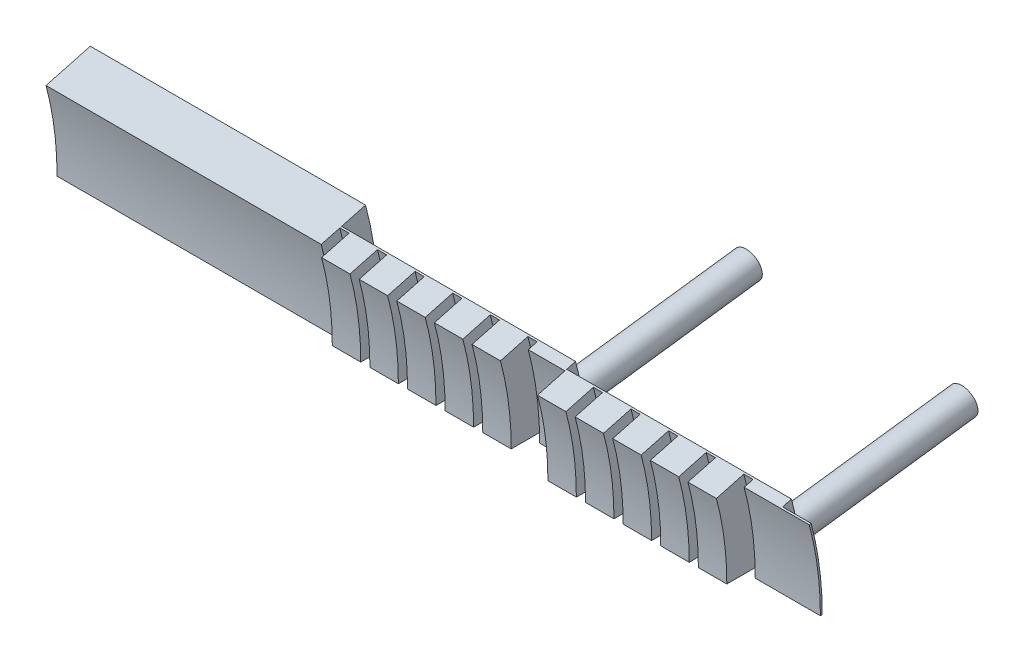
SolidWorks part; units mm, degrees
ref_plane "Front Plane" through (0, 0, 0) normal (0, 0, 1) x (1, 0, 0)
ref_plane "Top Plane" through (0, 0, 0) normal (0, 1, 0) x (1, 0, 0)
ref_plane "Right Plane" through (0, 0, 0) normal (1, 0, 0) x (0, 0, -1)
sketch "Sketch1" plane through (0, 0, 0) normal (0, 1, 0) x (1, 0, 0)
  line L0 (0, 0) -> (6.3693, 0) construction
  line L1 (0.254, 9.525) -> (0.254, 8.7376)
  line L2 (0.254, 8.7376) -> (1.0414, 8.7376)
  line L3 (1.0414, 8.7376) -> (1.0414, 9.525)
  line L4 (1.0414, 9.525) -> (1.2954, 9.525)
  line L5 (1.2954, 9.525) -> (1.2954, 8.7376)
  line L6 (1.2954, 8.7376) -> (2.0828, 8.7376)
  line L7 (2.0828, 8.7376) -> (2.0828, 9.525)
  line L8 (2.0828, 9.525) -> (2.3368, 9.525)
  line L9 (2.3368, 9.525) -> (2.3368, 8.7376)
  line L10 (2.3368, 8.7376) -> (3.1242, 8.7376)
  line L11 (3.1242, 8.7376) -> (3.1242, 9.525)
  line L12 (3.1242, 9.525) -> (3.3782, 9.525)
  line L13 (3.3782, 9.525) -> (3.3782, 8.7376)
  line L14 (3.3782, 8.7376) -> (4.1656, 8.7376)
  line L15 (4.1656, 8.7376) -> (4.1656, 9.525)
  line L16 (4.1656, 9.525) -> (4.4196, 9.525)
  line L17 (4.4196, 9.525) -> (4.4196, 8.7376)
  line L18 (4.4196, 8.7376) -> (5.207, 8.7376)
  line L19 (5.207, 8.7376) -> (5.207, 9.525)
  line L20 (5.207, 9.525) -> (5.461, 9.525)
  line L21 (5.461, 9.525) -> (5.461, 9.271)
  line L22 (5.461, 9.271) -> (6.477, 9.271)
  line L23 (6.477, 9.271) -> (6.477, 8.4836)
  line L24 (6.477, 8.4836) -> (7.2644, 8.4836)
  line L25 (7.2644, 8.4836) -> (7.2644, 9.271)
  line L26 (7.2644, 9.271) -> (7.5184, 9.271)
  line L27 (7.5184, 9.271) -> (7.5184, 8.4836)
  line L28 (7.5184, 8.4836) -> (8.3058, 8.4836)
  line L29 (8.3058, 8.4836) -> (8.3058, 9.271)
  line L30 (8.3058, 9.271) -> (8.5598, 9.271)
  line L31 (8.5598, 9.271) -> (8.5598, 8.4836)
  line L32 (8.5598, 8.4836) -> (9.3472, 8.4836)
  line L33 (9.3472, 8.4836) -> (9.3472, 9.271)
  line L34 (9.3472, 9.271) -> (9.6012, 9.271)
  line L35 (9.6012, 9.271) -> (9.6012, 8.4836)
  line L36 (9.6012, 8.4836) -> (10.3886, 8.4836)
  line L37 (10.3886, 8.4836) -> (10.3886, 9.271)
  line L38 (10.3886, 9.271) -> (10.6426, 9.271)
  line L39 (10.6426, 9.271) -> (10.6426, 8.4836)
  line L40 (10.6426, 8.4836) -> (11.43, 8.4836)
  line L41 (11.43, 8.4836) -> (11.43, 9.271)
  line L42 (11.43, 9.271) -> (11.684, 9.271)
  line L43 (11.684, 9.271) -> (11.684, 9.017)
  line L44 (11.684, 9.017) -> (12.7, 9.017)
  line L131 (0.254, 9.525) -> (0, 9.525)
  line L132 (0, 0) -> (0, 9.525) construction
  line L139 (6.477, 9.5758) -> (6.477, 9.3218)
  line L145 (12.7, 9.3218) -> (12.7, 9.0678)
  line L166 (0, 9.525) -> (0, 8.9916)
  line L167 (0, 8.9916) -> (-7.62, 8.9916)
  line L168 (-7.62, 8.9916) -> (-7.62, 10.2616)
  line L169 (6.477, 9.3218) -> (12.7, 9.3218)
  line L170 (6.477, 9.5758) -> (0, 9.5758)
  line L171 (-7.62, 10.2616) -> (0, 10.2616)
  line L172 (0, 10.2616) -> (0, 9.5758)
  line L173 (12.7, 9.0678) -> (13.4874, 9.0678)
  line L174 (13.4874, 9.0678) -> (13.4874, 9.017)
  line L175 (13.4874, 9.017) -> (12.7, 9.017)
  dimension "D1" = 0.254
  dimension "D2" = 0.7874
  dimension "D3" = 0.7874
  dimension "D4" = 1.016
  dimension "D5" = 0.254
  dimension "D6" = 9.525
  dimension "D9" = 1.27
  dimension "D10" = 0.254
  dimension "D11" = 7.62
  dimension "D12" = 0.254
  dimension "D16" = 0.7874
revolve "Revolve1" add sketch "Sketch1" angle 15 about L0
ref_plane "Plane1" through (0, 0, 0) normal (0, -0.9914, -0.1305) x (-1, 0, 0)
ref_plane "Plane2" through (0, 1.2499, -9.4939) normal (0, 0.1305, -0.9914) x (-1, 0, 0)
ref_plane "Plane3" through (0, 1.2167, -9.2421) normal (0, 0.1305, -0.9914) x (-1, 0, 0)
sketch "Sketch2" plane through (0, 1.2499, -9.4939) normal (0, 0.1305, -0.9914) x (-1, 0, 0)
  line L0 (-5.461, -1.2101) -> (-5.461, 1.2101) construction
  line L1 (-6.477, 1.2499) -> (-6.477, -1.2499) construction
  line L2 (-5.461, -1.2101) -> (-5.461, 1.2101) construction
  line L3 (-6.477, 1.2499) -> (-6.477, -1.2499) construction
  line L4 (-6.477, 0) -> (-5.461, 0) construction
  circle A0 centre (-5.969, 0) radius 0.3937
  point P6 (0, 0)
  dimension "D1" = 0.7874
extrude "Boss-Extrude2" add sketch "Sketch2" along normal blind 5.08 and the other way blind 0.127 separate body contours A0
sketch "Sketch3" plane through (0, 1.2167, -9.2421) normal (0, 0.1305, -0.9914) x (-1, 0, 0)
  line L0 (-11.684, -1.177) -> (-11.684, 1.177) construction
  line L1 (-12.7, 1.1836) -> (-12.7, -1.1836) construction
  line L2 (-11.684, -1.177) -> (-11.684, 1.177) construction
  line L3 (-12.7, 1.1836) -> (-12.7, -1.1836) construction
  line L4 (-12.7, 0) -> (-11.684, 0) construction
  circle A0 centre (-12.192, 0) radius 0.3937
  dimension "D1" = 0.7874
extrude "Boss-Extrude3" add sketch "Sketch3" along normal blind 5.08 and the other way up to surface
equation "\"0.2n\"=0.5"
